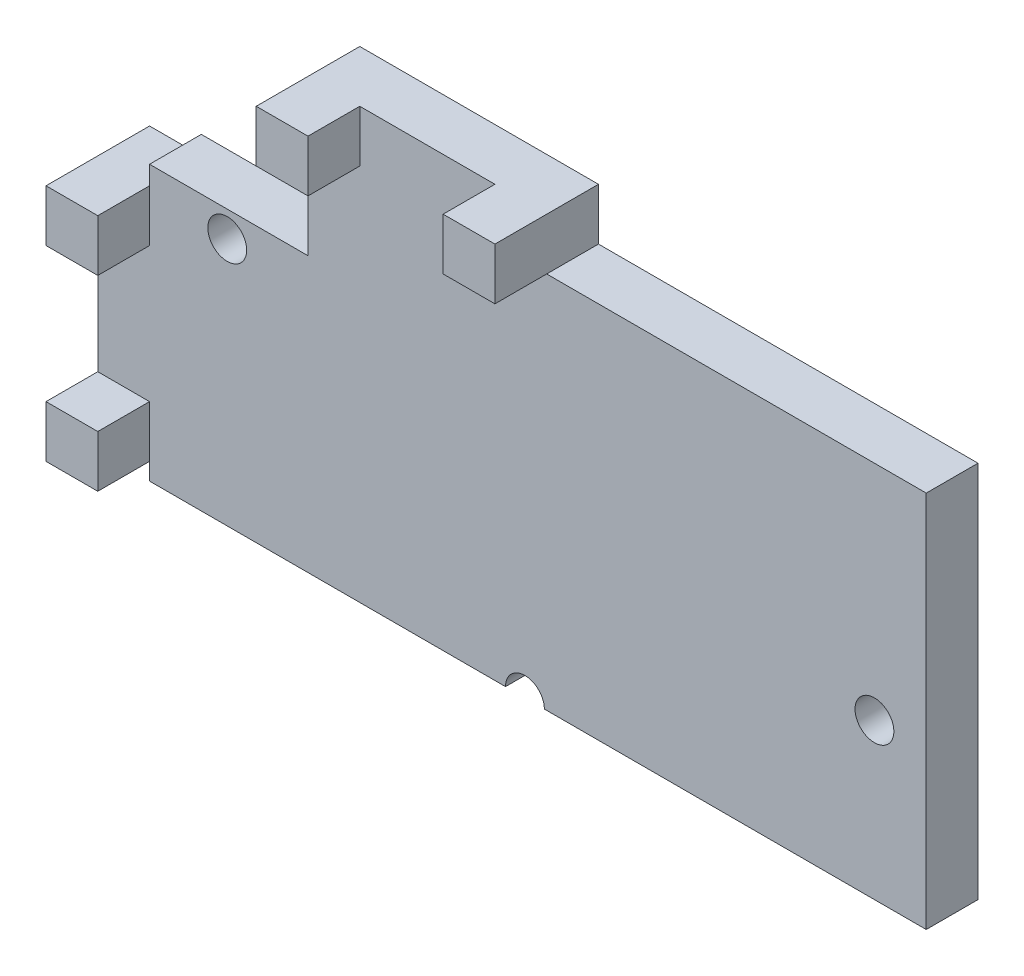
SolidWorks part; units mm, degrees
ref_plane "Front Plane" through (0, 0, 0) normal (0, 0, 1) x (1, 0, 0)
ref_plane "Top Plane" through (0, 0, 0) normal (0, 1, 0) x (1, 0, 0)
ref_plane "Right Plane" through (0, 0, 0) normal (1, 0, 0) x (0, 0, -1)
sketch "Sketch1" plane through (0, 0, 0) normal (0, 0, 1) x (1, 0, 0)
  line L1 (-5.5946, 3.8135) -> (9.4054, 3.8135)
  line L2 (-5.5946, 3.8135) -> (-5.5946, -3.4865)
  line L3 (-5.5946, -3.4865) -> (9.4054, -3.4865)
  line L4 (9.4054, 3.8135) -> (9.4054, -3.4865)
  dimension "D1" = 15
  dimension "D2" = 7.3
extrude "Base-Extrude1" add sketch "Sketch1" along normal blind 1
sketch "Notch" plane through (0, 0, 0) normal (0, 0, -1) x (-1, 0, 0)
  line L1 (5.5946, 3.8135) -> (2.5346, 3.8135)
  line L2 (5.5946, 3.8135) -> (5.5946, 1.8135)
  line L3 (5.5946, 1.8135) -> (2.5346, 1.8135)
  line L4 (2.5346, 3.8135) -> (2.5346, 1.8135)
  dimension "D1" = 3.06
  dimension "D2" = 2
extrude "Cut-Extrude1" cut sketch "Notch" against normal blind 1
sketch "Sketch5" plane through (0, 0, 1) normal (0, 0, 1) x (1, 0, 0)
  line L1 (-2.5346, 3.8135) -> (2.0754, 3.8135)
  line L2 (-2.5346, 3.8135) -> (-2.5346, 4.8135)
  line L3 (-2.5346, 4.8135) -> (2.0754, 4.8135)
  line L4 (2.0754, 3.8135) -> (2.0754, 4.8135)
  dimension "D1" = 1
  dimension "D2" = 4.61
extrude "Top-LED-Extrude" add sketch "Sketch5" against normal blind 1
sketch "Sketch6" plane through (0, 0, 1) normal (0, 0, 1) x (1, 0, 0)
  line L1 (-2.5346, 4.8135) -> (-1.5346, 4.8135)
  line L2 (-2.5346, 4.8135) -> (-2.5346, 3.8135)
  line L3 (-2.5346, 3.8135) -> (-1.5346, 3.8135)
  line L4 (-1.5346, 4.8135) -> (-1.5346, 3.8135)
  line L5 (2.0754, 4.8135) -> (2.0754, 3.8135)
  line L6 (2.0754, 3.8135) -> (1.0754, 3.8135)
  line L7 (1.0754, 3.8135) -> (1.0754, 4.8135)
  line L8 (2.0754, 4.8135) -> (-2.5346, 4.8135) construction
  line L9 (1.0754, 4.8135) -> (2.0754, 4.8135)
  dimension "D1" = 1
  dimension "D2" = 1
  dimension "D3" = 1
extrude "Top-Clamp" add sketch "Sketch6" along normal blind 1
sketch "Sketch7" plane through (-5.5946, 0, 0) normal (-1, 0, 0) x (0, 0, 1)
  line L0 (0, -3.1565) -> (1, -3.1565)
  line L1 (1, -3.1565) -> (1, 1.4535)
  line L2 (1, 1.8135) -> (1, -3.4865) construction
  line L3 (1, 1.4535) -> (0, 1.4535)
  line L4 (0, 1.8135) -> (0, -3.4865) construction
  line L5 (0, 1.4535) -> (0, -3.1565)
  line L6 (1, -3.4865) -> (0, -3.4865) construction
  dimension "D1" = 0.33
  dimension "D2" = 4.61
extrude "Side-LED-Extrude" add sketch "Sketch7" along normal blind 1
sketch "Sketch8" plane through (0, 0, 1) normal (0, 0, 1) x (1, 0, 0)
  line L0 (-6.5946, -3.1565) -> (-5.5946, -3.1565) construction
  line L1 (-6.5946, -3.1565) -> (-5.5946, -3.1565)
  line L2 (-6.5946, -3.1565) -> (-6.5946, -2.1565)
  line L3 (-6.5946, -2.1565) -> (-5.5946, -2.1565)
  line L4 (-5.5946, -3.1565) -> (-5.5946, -2.1565)
  line L5 (-6.5946, 1.4535) -> (-5.5946, 1.4535)
  line L6 (-6.5946, 1.4535) -> (-6.5946, 0.4535)
  line L7 (-6.5946, 0.4535) -> (-5.5946, 0.4535)
  line L8 (-5.5946, 1.4535) -> (-5.5946, 0.4535)
  dimension "D1" = 1
  dimension "D2" = 1
  dimension "D3" = 1
  dimension "D4" = 1
extrude "Side-Clamp" add sketch "Sketch8" along normal blind 1
sketch "Sketch9" plane through (0, 0, 0) normal (0, 0, -1) x (-1, 0, 0)
  line L0 (5.5946, 1.8135) -> (5.5946, 1.4535) construction
  line L1 (-9.4054, 3.8135) -> (-2.0754, 3.8135) construction
  line L2 (5.5946, -3.4865) -> (-9.4054, -3.4865) construction
  line L3 (-9.4054, -3.4865) -> (-9.4054, 3.8135) construction
  circle A0 centre (-8.4054, -0.4865) radius 0.375
  circle A1 centre (4.0946, 1.3135) radius 0.375
  circle A2 centre (-1.6554, -3.4865) radius 0.375
  point P12 (5.5946, 1.6335)
  dimension "D1" = 0.75
  dimension "D2" = 1.5
  dimension "D3" = 2.5
  dimension "D4" = 0
  dimension "D6" = 1
  dimension "D7" = 3
  dimension "D5" = 7.75
extrude "ScrewHoles" cut sketch "Sketch9" against normal blind 1
